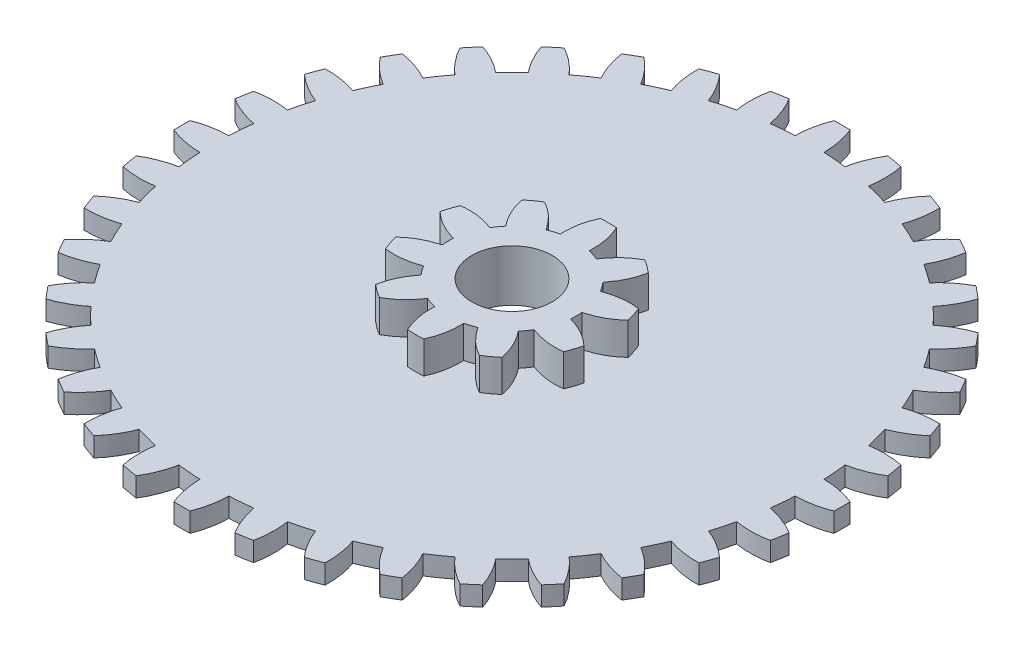
SolidWorks part; units mm, degrees
ref_plane "Front Plane" through (0, 0, 0) normal (0, 0, 1) x (1, 0, 0)
ref_plane "Top Plane" through (0, 0, 0) normal (0, 1, 0) x (1, 0, 0)
ref_plane "Right Plane" through (0, 0, 0) normal (1, 0, 0) x (0, 0, -1)
sketch "Sketch1" plane through (0, 0, 0) normal (0, 1, 0) x (1, 0, 0)
  circle A0 centre (0, 0) radius 3.7
  dimension "D1" = 7.4
extrude "Boss-Extrude1" add sketch "Sketch1" along normal blind 0.24
sketch "Sketch3" plane through (0, 0, 0) normal (0, 1, 0) x (1, 0, 0)
  line L0 (0, 0) -> (0, -4.3179) construction
  circle A0 centre (0, 0) radius 3.7 construction
  arc A1 (-0.18, -3.6956) -> (0.18, -3.6956) centre (0, 0) ccw
  arc A2 (-0.1, -4.0988) -> (0.1, -4.0988) centre (0, 0) ccw
  spline S0 degree 3 poles (-0.1, -4.0988) (-0.1433, -3.9958) (-0.1797, -3.8392) (-0.18, -3.6956) knots 0 0 0 0 1 1 1 1
  spline S1 degree 3 poles (0.1, -4.0988) (0.1433, -3.9958) (0.1797, -3.8392) (0.18, -3.6956) knots 0 0 0 0 1 1 1 1
  dimension "D1" = 8.2
  dimension "D2" = 0.18
  dimension "D3" = 0.1
extrude "Boss-Extrude2" add sketch "Sketch3" along normal blind 0.24
pattern_circular "CirPattern1" count 36 over 360 about axis through (0, 0.24, 0) along (0, -1, 0) of "Boss-Extrude2"
sketch "Sketch4" plane through (0, 0.24, 0) normal (0, 1, 0) x (1, 0, 0)
  circle A0 centre (0, 0) radius 0.8
  dimension "D1" = 1.6
extrude "Boss-Extrude3" add sketch "Sketch4" along normal blind 0.4
sketch "Sketch5" plane through (0, 0.24, 0) normal (0, 1, 0) x (1, 0, 0)
  line L0 (0, 0) -> (0, -1.2338) construction
  arc A0 (-0.1, -1.1958) -> (0.1, -1.1958) centre (0, 0) ccw
  circle A3 centre (0, 0) radius 0.8 construction
  circle A4 centre (0, 0) radius 0.8 construction
  arc A5 (-0.18, -0.7795) -> (0.18, -0.7795) centre (0, 0) ccw
  spline S0 degree 3 poles (-0.18, -0.7795) (-0.1863, -0.9717) (-0.1502, -1.0855) (-0.1, -1.1958) knots 0 0 0 0 1 1 1 1
  spline S1 degree 3 poles (0.18, -0.7795) (0.1863, -0.9717) (0.1502, -1.0855) (0.1, -1.1958) knots 0 0 0 0 1 1 1 1
  dimension "D1" = 2.4
  dimension "D2" = 0.18
  dimension "D3" = 0.1
extrude "Boss-Extrude4" add sketch "Sketch5" along normal blind 0.4
pattern_circular "CirPattern2" count 10 over 360 about axis through (0, 0.64, 0) along (0, -1, 0) of "Boss-Extrude4"
sketch "Sketch6" plane through (0, 0.64, 0) normal (0, 1, 0) x (1, 0, 0)
  circle A0 centre (0, 0) radius 0.5
  dimension "D1" = 1
extrude "Cut-Extrude1" cut sketch "Sketch6" against normal through all
